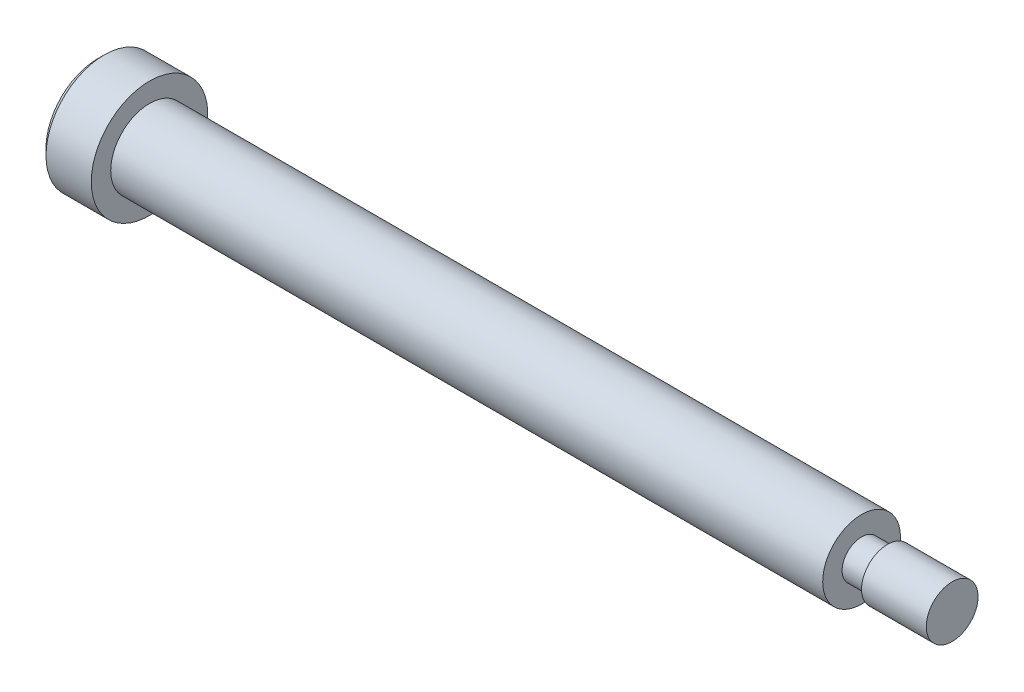
SolidWorks part; units mm, degrees
material "Plain Carbon Steel"
ref_plane "Front Plane" through (0, 0, 0) normal (0, 0, 1) x (1, 0, 0)
ref_plane "Top Plane" through (0, 0, 0) normal (0, 1, 0) x (1, 0, 0)
ref_plane "Right Plane" through (0, 0, 0) normal (1, 0, 0) x (0, 0, -1)
sketch "Sketch1" plane through (0, 0, 0) normal (0, 0, 1) x (1, 0, 0)
  line L0 (0, 3) -> (55, 3)
  line L1 (55, 3) -> (55, 1.5)
  line L2 (55, 1.5) -> (57, 1.5)
  line L3 (57, 1.5) -> (57, 2)
  line L4 (57, 2) -> (62, 2)
  line L5 (62, 2) -> (62, 0)
  line L6 (62, 0) -> (-4, 0)
  line L7 (-4, 0) -> (-4, 4.5)
  line L8 (-4, 4.5) -> (0, 4.5)
  line L9 (0, 4.5) -> (0, 3)
  line L10 (-15.4482, 0) -> (78.4971, 0) construction
  dimension "D1" = 4
  dimension "D2" = 6
  dimension "D3" = 55
  dimension "D4" = 3
  dimension "D5" = 7
  dimension "D6" = 2
  dimension "D7" = 9
  dimension "D8" = 4
revolve "Revolve1" add sketch "Sketch1" angle 360 about L10
cosmetic thread "Cosmetic Thread1" parameters "D2"=3.22
chamfer "Chamfer2" distance 0.5 angle 45 1 edges at (-4, 0, 4.5)
sketch "Sketch2" plane through (-4, 0, 0) normal (-1, 0, 0) x (0, 0, 1)
  line L0 (0, 0) -> (0, 1.7321) construction
  line L1 (0, 1.7321) -> (-1.5, 0.866)
  line L2 (-1.5, 0.866) -> (-1.5, -0.866)
  line L3 (-1.5, -0.866) -> (0, -1.7321)
  line L4 (0, -1.7321) -> (1.5, -0.866)
  line L5 (1.5, -0.866) -> (1.5, 0.866)
  line L6 (1.5, 0.866) -> (0, 1.7321)
  line L7 (0, 1.7321) -> (0.0181, 1.7917) construction
  circle A0 centre (0, 0) radius 1.5 construction
  dimension "D1" = 3
extrude "Cut-Extrude1" cut sketch "Sketch2" against normal blind 2
